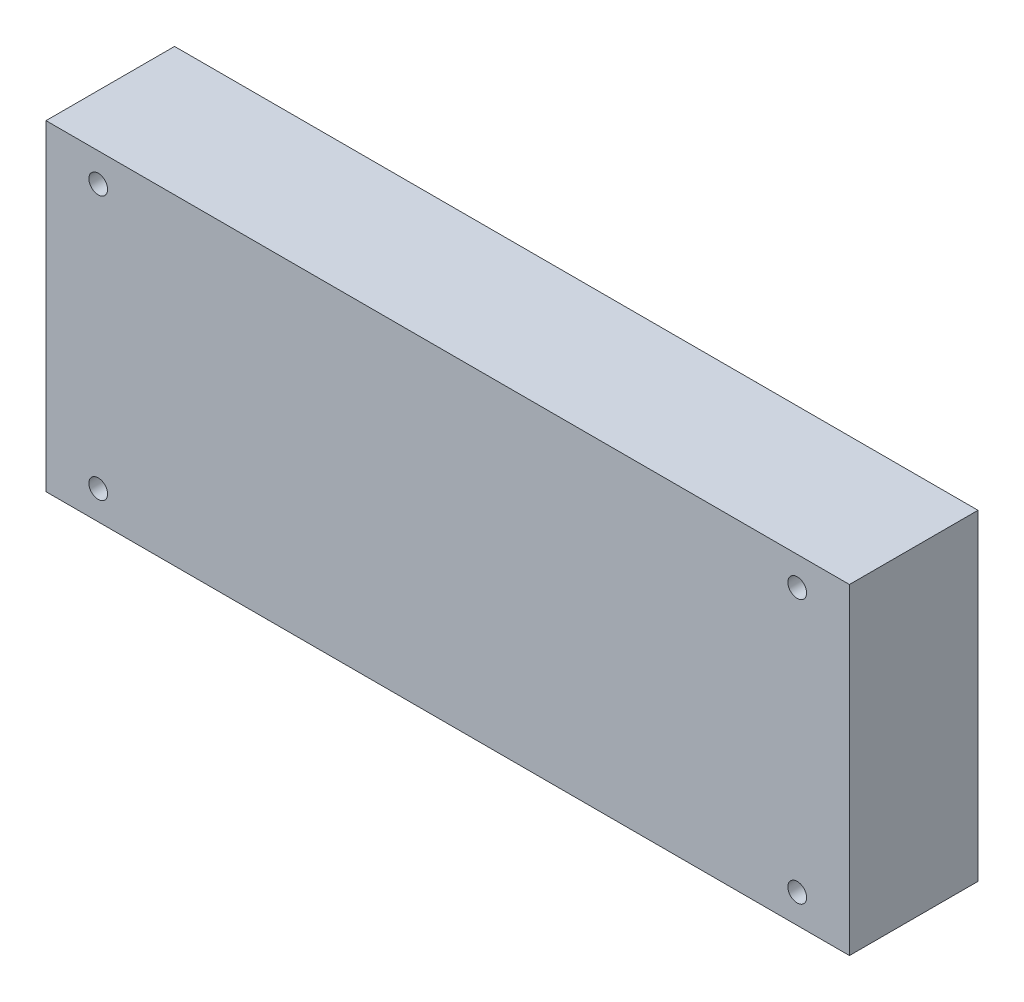
SolidWorks part; units mm, degrees
ref_plane "Front Plane" through (0, 0, 0) normal (0, 0, 1) x (1, 0, 0)
ref_plane "Top Plane" through (0, 0, 0) normal (0, 1, 0) x (1, 0, 0)
ref_plane "Right Plane" through (0, 0, 0) normal (1, 0, 0) x (0, 0, -1)
sketch "Sketch1" plane through (0, 0, 0) normal (0, 0, 1) x (1, 0, 0)
  line L1 (0, 0) -> (150, 0)
  line L2 (0, 0) -> (0, 60)
  line L3 (0, 60) -> (150, 60)
  line L4 (150, 0) -> (150, 60)
  line L5 (4.5, 56) -> (145.5, 56)
  line L6 (4.5, 56) -> (4.5, 4)
  line L7 (4.5, 4) -> (145.5, 4)
  line L8 (145.5, 56) -> (145.5, 4)
  point P9 (75, 60)
  point P10 (75, 56)
  point P11 (0, 30)
  point P12 (4.5, 30)
  dimension "D1" = 60
  dimension "D2" = 150
  dimension "D3" = 52
  dimension "D4" = 141
extrude "Boss-Extrude1" add sketch "Sketch1" along normal blind 20
sketch "Sketch2" plane through (0, 0, 20) normal (0, 0, 1) x (1, 0, 0)
  line L1 (0, 60) -> (150, 60)
  line L2 (0, 60) -> (0, 0)
  line L3 (0, 0) -> (150, 0)
  line L4 (150, 60) -> (150, 0)
extrude "Boss-Extrude2" add sketch "Sketch2" along normal blind 4
sketch "Sketch3" plane through (0, 0, 0) normal (0, -1, 0) x (1, 0, 0)
  line L1 (9, 17) -> (141, 17)
  line L2 (9, 17) -> (9, 0)
  line L3 (9, 0) -> (141, 0)
  line L4 (141, 17) -> (141, 0)
  line L5 (0, 24) -> (150, 24) construction
  line L6 (0, 0) -> (150, 0) construction
  point P4 (75, 17)
  point P7 (75, 24)
  dimension "D1" = 132
  dimension "D2" = 17
extrude "Cut-Extrude1" cut sketch "Sketch3" against normal blind 16
sketch "Sketch4" plane through (0, 0, 20) normal (0, 0, -1) x (-1, 0, 0)
  line L0 (-75, 56) -> (-75, 38.9443) construction
  line L1 (-145.5, 56) -> (-4.5, 56) construction
  line L2 (-145.5, 30) -> (-124.6713, 30) construction
  line L3 (-145.5, 4) -> (-145.5, 56) construction
  circle A0 centre (-140.25, 54.625) radius 1.75
  circle A1 centre (-9.75, 54.625) radius 1.75
  circle A2 centre (-9.75, 5.375) radius 1.75
  circle A3 centre (-140.25, 5.375) radius 1.75
  dimension "D1" = 3.5
  dimension "D2" = 130.5
  dimension "D3" = 49.25
extrude "Cut-Extrude3" cut sketch "Sketch4" against normal through all and the other way through all
sketch "Sketch5" plane through (0, 0, 0) normal (0, 0, -1) x (-1, 0, 0)
  line L0 (-75, 56) -> (-75, 45.5037) construction
  line L1 (-139.1675, 56) -> (-10.8325, 56) construction
  line L2 (-145.5, 30) -> (-123.6215, 30) construction
  line L3 (-145.5, 4) -> (-145.5, 56) construction
  circle A0 centre (-140.25, 5.375) radius 3
  circle A1 centre (-9.75, 5.375) radius 3
  circle A2 centre (-140.25, 54.625) radius 3
  circle A3 centre (-9.75, 54.625) radius 3
  dimension "D1" = 6
extrude "Cut-Extrude4" cut sketch "Sketch5" against normal up to vertex
